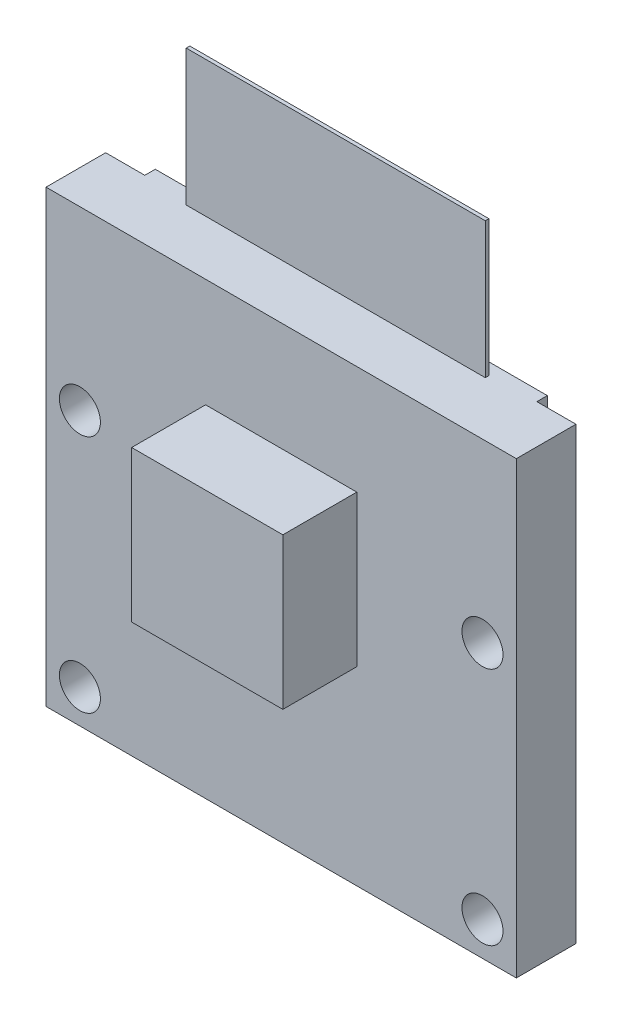
SolidWorks part; units mm, degrees
ref_plane "Front Plane" through (0, 0, 0) normal (0, 0, 1) x (1, 0, 0)
ref_plane "Top Plane" through (0, 0, 0) normal (0, 1, 0) x (1, 0, 0)
ref_plane "Right Plane" through (0, 0, 0) normal (1, 0, 0) x (0, 0, -1)
sketch "Sketch1" plane through (0, 0, 0) normal (0, 0, 1) x (1, 0, 0)
  line L1 (-25.8271, 0.9112) -> (-0.7827, 0.9112)
  line L2 (-25.8271, 0.9112) -> (-25.8271, 24.8634)
  line L3 (-25.8271, 24.8634) -> (-0.7827, 24.8634)
  line L4 (-0.7827, 0.9112) -> (-0.7827, 24.8634)
  dimension "D1" = 25.0444
  dimension "D2" = 23.9522
extrude "Boss-Extrude1" add sketch "Sketch1" along normal blind 3.175
sketch "Sketch2" plane through (0, 0, 3.175) normal (0, 0, 1) x (1, 0, 0)
  line L0 (-25.8271, 0.9112) -> (-0.7827, 0.9112) construction
  line L1 (-0.7827, 0.9112) -> (-0.7827, 24.8634) construction
  line L2 (-13.3049, 24.8634) -> (-13.3049, 0.9112) construction
  line L3 (-0.7827, 24.8634) -> (-25.8271, 24.8634) construction
  circle A0 centre (-2.5861, 2.7146) radius 1.0922
  circle A1 centre (-2.5861, 15.4654) radius 1.0922
  circle A2 centre (-24.0237, 2.7146) radius 1.0922
  circle A3 centre (-24.0237, 15.4654) radius 1.0922
  dimension "D1" = 1.8034
  dimension "D3" = 1.8034
  dimension "D4" = 14.5542
  dimension "D2" = 1.8034
extrude "Cut-Extrude1" cut sketch "Sketch2" against normal blind 3.175
sketch "Sketch3" plane through (0, 0, 3.175) normal (0, 0, 1) x (1, 0, 0)
  line L0 (-13.3049, 24.8634) -> (-13.3049, 0.9112) construction
  line L1 (-17.3308, 19.0722) -> (-9.279, 19.0722)
  line L2 (-17.3308, 19.0722) -> (-17.3308, 11.0204)
  line L3 (-17.3308, 11.0204) -> (-9.279, 11.0204)
  line L4 (-9.279, 19.0722) -> (-9.279, 11.0204)
  line L5 (-0.7827, 24.8634) -> (-25.8271, 24.8634) construction
  line L6 (-25.8271, 0.9112) -> (-0.7827, 0.9112) construction
  line L7 (-13.3049, 19.0722) -> (-13.3049, 11.0204) construction
  dimension "D1" = 8.0518
  dimension "D2" = 8.0518
  dimension "D3" = 0
  dimension "D4" = 5.7912
extrude "Boss-Extrude2" add sketch "Sketch3" along normal blind 3.937
sketch "Sketch4" plane through (0, 0, 0) normal (0, 0, -1) x (-1, 0, 0)
  line L0 (0.7827, 24.8634) -> (25.8271, 24.8634) construction
  line L1 (2.8655, 24.8634) -> (23.7443, 24.8634)
  line L2 (2.8655, 24.8634) -> (2.8655, 19.3262)
  line L3 (2.8655, 19.3262) -> (23.7443, 19.3262)
  line L4 (23.7443, 24.8634) -> (23.7443, 19.3262)
  line L5 (13.3049, 24.8634) -> (13.3049, 19.3262) construction
  line L6 (13.3049, 0.9112) -> (13.3049, 24.8634) construction
  line L7 (25.8271, 0.9112) -> (0.7827, 0.9112) construction
  dimension "D1" = 20.8788
  dimension "D2" = 5.5372
  dimension "D3" = 0
extrude "Boss-Extrude3" add sketch "Sketch4" along normal blind 0.5588
sketch "Sketch5" plane through (0, 24.8634, 0) normal (0, 1, 0) x (1, 0, 0)
  line L0 (-13.3049, 0.5588) -> (-13.3049, -2.3744) construction
  line L1 (-21.2678, -0.0762) -> (-5.342, -0.0762)
  line L2 (-21.2678, -0.0762) -> (-21.2678, -0.2682)
  line L3 (-21.2678, -0.2682) -> (-5.342, -0.2682)
  line L4 (-5.342, -0.0762) -> (-5.342, -0.2682)
  line L5 (-23.7443, 0.5588) -> (-2.8655, 0.5588) construction
  line L6 (-13.3049, -0.0762) -> (-13.3049, -1.1458) construction
  dimension "D1" = 15.9258
  dimension "D2" = 0
  dimension "D3" = 0.635
extrude "Boss-Extrude4" add sketch "Sketch5" along normal blind 7.239
